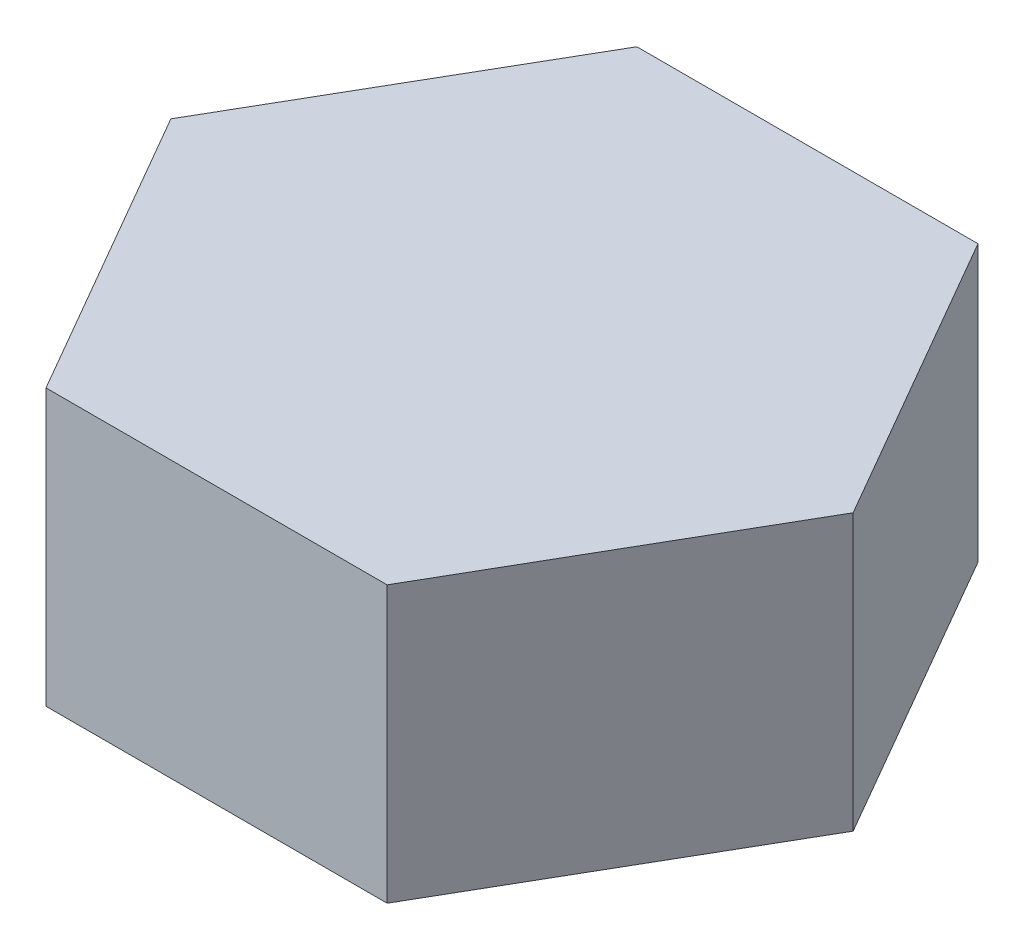
SolidWorks part; units mm, degrees
ref_plane "Front Plane" through (0, 0, 0) normal (0, 0, 1) x (1, 0, 0)
ref_plane "Top Plane" through (0, 0, 0) normal (0, 1, 0) x (1, 0, 0)
ref_plane "Right Plane" through (0, 0, 0) normal (1, 0, 0) x (0, 0, -1)
sketch "Sketch1" plane through (0, 0, 0) normal (0, 1, 0) x (1, 0, 0)
  line L0 (0, 0) -> (1.2148, 0) construction
  line L1 (2.5981, 0) -> (1.299, 2.25)
  line L2 (1.299, 2.25) -> (-1.299, 2.25)
  line L3 (-1.299, 2.25) -> (-2.5981, 0)
  line L4 (-2.5981, 0) -> (-1.299, -2.25)
  line L5 (-1.299, -2.25) -> (1.299, -2.25)
  line L6 (1.299, -2.25) -> (2.5981, 0)
  circle A0 centre (0, 0) radius 2.25 construction
  dimension "D1" = 5.1962
extrude "Boss-Extrude1" add sketch "Sketch1" along normal blind 2.1
